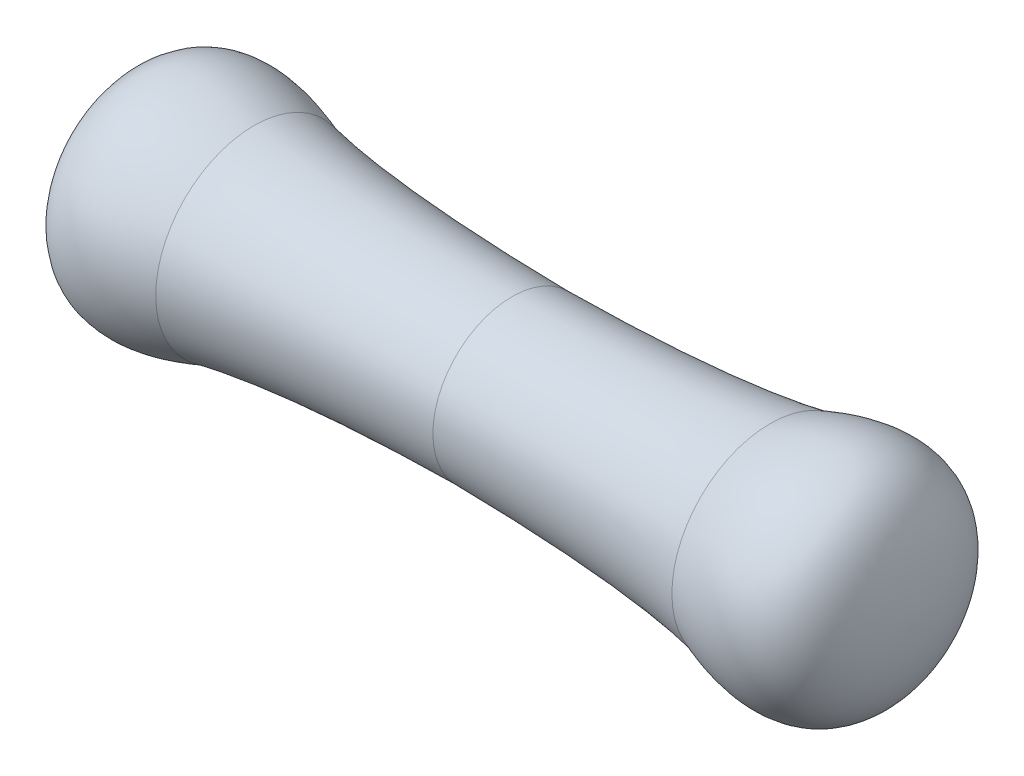
SolidWorks part; units mm, degrees
ref_plane "Plan de face" through (0, 0, 0) normal (0, 0, 1) x (1, 0, 0)
ref_plane "Plan de dessus" through (0, 0, 0) normal (0, 1, 0) x (1, 0, 0)
ref_plane "Plan de droite" through (0, 0, 0) normal (1, 0, 0) x (0, 0, -1)
sketch "Esquisse1" plane through (0, 0, 0) normal (0, 0, 1) x (1, 0, 0)
  line L0 (0, 0) -> (3.9949, 0) construction
  line L1 (0, -1) -> (3.9949, -1) construction
  line L2 (0, 1) -> (3.9949, 1) construction
  line L3 (0, -1.5525) -> (0, 2.2525) construction
  line L4 (3.5, -1.5525) -> (3.5, 2.2525) construction
  line L5 (-3.5, -1.5525) -> (-3.5, 2.2525) construction
  line L6 (-3.5, 0) -> (3.5, 0)
  spline S0 degree 2 poles (3.5, 0) (3.4675, 1.3175) (2.2458, 0.8544) knots 0 0 0 1 1 1
  spline S1 degree 2 poles (2.2458, 0.8544) (1.5073, 0.7046) (0, 0.6884) knots 0 0 0 1 1 1
  spline S2 degree 2 poles (-3.5, 0) (-3.4675, 1.3175) (-2.2458, 0.8544) knots 0 0 0 1 1 1
  spline S3 degree 2 poles (-2.2458, 0.8544) (-1.5073, 0.7046) (0, 0.6884) knots 0 0 0 1 1 1
  dimension "D1" = 1
  dimension "D3" = 3.5
  dimension "D2" = 1
  dimension "D4" = 3.5
revolve "Révolution1" add sketch "Esquisse1" angle 360 about L6
